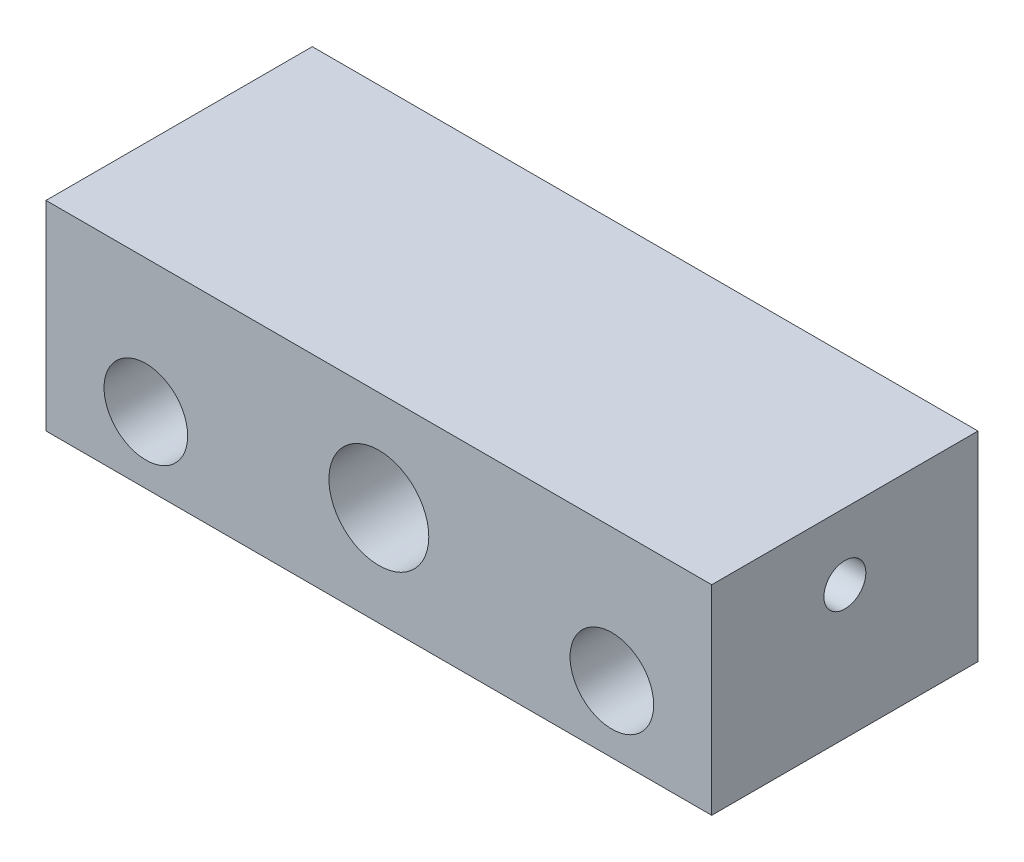
SolidWorks part; units mm, degrees
ref_plane "Front Plane" through (0, 0, 0) normal (0, 0, 1) x (1, 0, 0)
ref_plane "Top Plane" through (0, 0, 0) normal (0, 1, 0) x (1, 0, 0)
ref_plane "Right Plane" through (0, 0, 0) normal (1, 0, 0) x (0, 0, -1)
sketch "Sketch1" plane through (0, 0, 0) normal (0, 0, 1) x (1, 0, 0)
  line L0 (0, 0) -> (0, -9.525) construction
  line L1 (-31.75, 9.525) -> (31.75, 9.525)
  line L2 (-31.75, 9.525) -> (-31.75, -9.525)
  line L3 (-31.75, -9.525) -> (31.75, -9.525)
  line L4 (31.75, 9.525) -> (31.75, -9.525)
  line L5 (-31.75, 9.525) -> (31.75, -9.525) construction
  line L6 (-31.75, -9.525) -> (31.75, 9.525) construction
  line L7 (-22.225, -3.175) -> (0, -3.175) construction
  line L8 (22.225, -3.175) -> (0, -3.175) construction
  circle A0 centre (0, 0) radius 4.7625
  circle A1 centre (-22.225, -3.175) radius 3.9878
  circle A2 centre (22.225, -3.175) radius 3.9878
  point P0 (0, 0)
  dimension "D3" = 9.525
  dimension "D5" = 7.9756
  dimension "D1" = 19.05
  dimension "D2" = 63.5
  dimension "D4" = 44.45
  dimension "D6" = 6.35
extrude "Boss-Extrude1" add sketch "Sketch1" against normal blind 25.4
sketch "Sketch2" plane through (-31.75, 0, 0) normal (-1, 0, 0) x (0, 0, 1)
  line L0 (-12.7, -9.525) -> (-12.7, 9.525) construction
  line L1 (-25.4, -9.525) -> (0, -9.525) construction
  line L2 (-25.4, 9.525) -> (0, 9.525) construction
  circle A0 centre (-12.7, 3.175) radius 2
  dimension "D1" = 4
  dimension "D2" = 6.35
extrude "Cut-Extrude1" cut sketch "Sketch2" against normal blind 6.35
ref_plane "Plane1" through (0, 0, 0) normal (-1, 0, 0) x (0, 0, 1)
mirror "Mirror1" about plane through (0, 0, 0) normal (-1, 0, 0) of "Cut-Extrude1"
